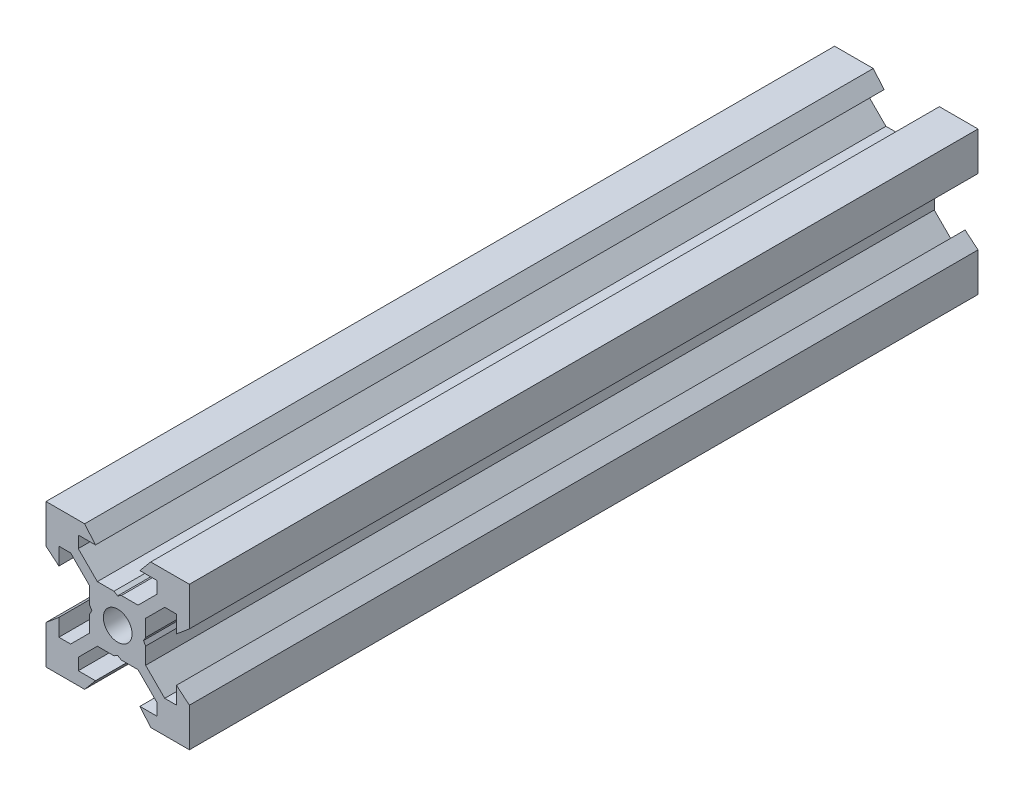
SolidWorks part; units mm, degrees
ref_plane "Front Plane" through (0, 0, 0) normal (0, 0, 1) x (1, 0, 0)
ref_plane "Top Plane" through (0, 0, 0) normal (0, 1, 0) x (1, 0, 0)
ref_plane "Right Plane" through (0, 0, 0) normal (1, 0, 0) x (0, 0, -1)
sketch "Sketch1" plane through (0, 0, 0) normal (0, 0, 1) x (1, 0, 0)
  line L0 (10, 10) -> (4.6104, 10) construction
  line L1 (10, 10) -> (10, 4.6104) construction
  line L2 (10, -10) -> (10, -4.6104) construction
  line L3 (10, -10) -> (4.6104, -10) construction
  line L4 (10, 10) -> (10, 4.6104)
  line L5 (6.5607, 5.5) -> (8.2, 5.5)
  line L6 (5.5, 8.2) -> (5.5, 6.5607)
  line L7 (10, 10) -> (4.6104, 10)
  line L8 (10, 10) -> (10, 4.6104)
  line L9 (6.5607, 5.5) -> (3.9, 2.8393)
  line L10 (5.5, 6.5607) -> (2.8393, 3.9)
  line L11 (10, 4.6104) -> (8.2, 3.1)
  line L12 (4.6104, 10) -> (3.1, 8.2)
  line L13 (8.2, 3.1) -> (8.2, 5.5)
  line L14 (3.1, 8.2) -> (5.5, 8.2)
  line L15 (-6.5607, 5.5) -> (-8.2, 5.5)
  line L16 (6.5607, -5.5) -> (8.2, -5.5)
  line L17 (3.1, -8.2) -> (5.5, -8.2)
  line L18 (8.2, -3.1) -> (8.2, -5.5)
  line L19 (4.6104, -10) -> (3.1, -8.2)
  line L20 (10, -4.6104) -> (8.2, -3.1)
  line L21 (0.5196, -3.9) -> (0, -3.6)
  line L22 (0.5196, 3.9) -> (0, 3.6)
  line L23 (3.6, 0) -> (3.9, -0.5196)
  line L24 (3.9, 0.5196) -> (3.6, 0)
  line L25 (3.9, 0.5196) -> (3.9, 2.8393)
  line L26 (2.8393, 3.9) -> (0.5196, 3.9)
  line L27 (3.9, -2.8393) -> (3.9, -0.5196)
  line L28 (2.8393, -3.9) -> (0.5196, -3.9)
  line L29 (5.5, -6.5607) -> (2.8393, -3.9)
  line L30 (6.5607, -5.5) -> (3.9, -2.8393)
  line L31 (10, -10) -> (10, -4.6104)
  line L32 (10, -10) -> (4.6104, -10)
  line L33 (5.5, -8.2) -> (5.5, -6.5607)
  line L34 (-6.5607, -5.5) -> (-8.2, -5.5)
  line L35 (10, -10) -> (10, -4.6104)
  line L36 (0, 0) -> (0, 8.2) construction
  line L37 (-10, -10) -> (-4.6104, -10) construction
  line L38 (-10, -10) -> (-10, -4.6104) construction
  line L39 (-10, 10) -> (-10, 4.6104) construction
  line L40 (-10, 10) -> (-4.6104, 10) construction
  line L41 (-10, -10) -> (-10, -4.6104)
  line L43 (-5.5, -8.2) -> (-5.5, -6.5607)
  line L44 (-10, -10) -> (-4.6104, -10)
  line L45 (-10, -10) -> (-10, -4.6104)
  line L46 (-6.5607, -5.5) -> (-3.9, -2.8393)
  line L47 (-5.5, -6.5607) -> (-2.8393, -3.9)
  line L48 (-2.8393, -3.9) -> (-0.5196, -3.9)
  line L49 (-3.9, -2.8393) -> (-3.9, -0.5196)
  line L50 (-2.8393, 3.9) -> (-0.5196, 3.9)
  line L51 (-3.9, 0.5196) -> (-3.9, 2.8393)
  line L52 (-3.9, 0.5196) -> (-3.6, 0)
  line L53 (-3.6, 0) -> (-3.9, -0.5196)
  line L54 (-0.5196, 3.9) -> (0, 3.6)
  line L55 (-0.5196, -3.9) -> (0, -3.6)
  line L56 (-10, -4.6104) -> (-8.2, -3.1)
  line L57 (-4.6104, -10) -> (-3.1, -8.2)
  line L58 (-8.2, -3.1) -> (-8.2, -5.5)
  line L59 (-3.1, -8.2) -> (-5.5, -8.2)
  line L60 (-10, -10) -> (10, -10) construction
  line L61 (-10, -10) -> (-10, 10) construction
  line L62 (-3.1, 8.2) -> (-5.5, 8.2)
  line L63 (-8.2, 3.1) -> (-8.2, 5.5)
  line L64 (-4.6104, 10) -> (-3.1, 8.2)
  line L65 (-10, 4.6104) -> (-8.2, 3.1)
  line L66 (-5.5, 6.5607) -> (-2.8393, 3.9)
  line L67 (-6.5607, 5.5) -> (-3.9, 2.8393)
  line L68 (-10, 10) -> (-10, 4.6104)
  line L69 (-10, 10) -> (-4.6104, 10)
  line L70 (-5.5, 8.2) -> (-5.5, 6.5607)
  line L71 (-10, 10) -> (10, 10) construction
  line L72 (-10, 10) -> (-10, 4.6104)
  line L73 (10, -10) -> (10, 10) construction
  line L74 (-10, -10) -> (10, 10) construction
  line L75 (-10, 10) -> (10, -10) construction
  circle A0 centre (0, 0) radius 2
  dimension "D7" = 4
  dimension "D1" = 20
  dimension "D2" = 5.3896
  dimension "D3" = 4.5
  dimension "D4" = 50
  dimension "D5" = 1.8
  dimension "D6" = 1.5104
  dimension "D8" = 5.5
  dimension "D9" = 120
  dimension "D10" = 0.3
  dimension "D11" = 2.3197
  dimension "D12" = 7.8
  dimension "D13" = 7.8
  dimension "D14" = 1.5
  dimension "D15" = 2.6607
extrude "Boss-Extrude1" add sketch "Sketch1" along normal mid plane 110 contours L70 L62 L64 L69 L68 L65 L63 L15 L67 L51 L52 L53 L49 L46 L34 L58 L56 L41 L44 L57 L59 L43 L47 L48 L55 L21 L28 L29 L33 L17 L19 L32 L31 L20 L18 L16 L30 L27 L23 L24 L25 L9 L5 L13 L11 L4 L7 L12 L14 L6 L10
